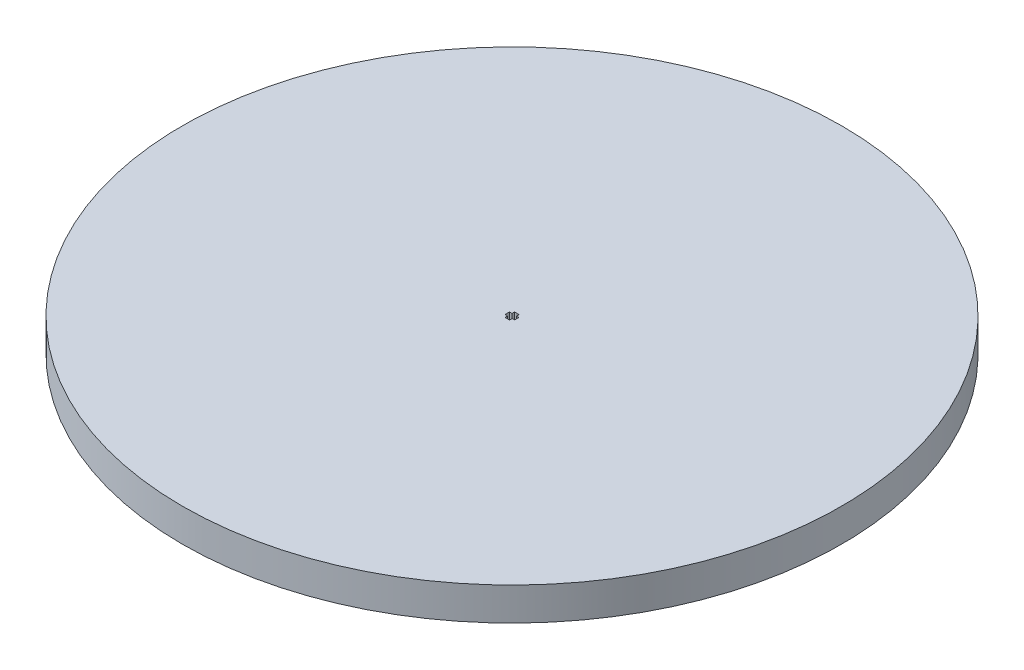
SolidWorks part; units mm, degrees
ref_plane "Front Plane" through (0, 0, 0) normal (0, 0, 1) x (1, 0, 0)
ref_plane "Top Plane" through (0, 0, 0) normal (0, 1, 0) x (1, 0, 0)
ref_plane "Right Plane" through (0, 0, 0) normal (1, 0, 0) x (0, 0, -1)
sketch "Sketch1" plane through (0, 0, 0) normal (0, 1, 0) x (1, 0, 0)
  line L1 (-102.886, 0) -> (102.886, 0) construction
  line L4 (-24.7302, 24.7302) -> (24.7302, -24.7302) construction
  line L5 (-31.3406, -31.3406) -> (31.3406, 31.3406) construction
  line L20 (-0.3381, -0.7219) -> (-0.3381, 0.7219)
  line L21 (-0.3381, 0.7219) -> (0.0122, 0.7219)
  line L22 (0, 0.3381) -> (-0.7219, 0.3381)
  line L23 (-0.7219, 0.3381) -> (-0.7219, -0.0122)
  line L24 (0.7329, 0.3136) -> (0.7211, -0.0365)
  line L25 (0.0114, 0.3379) -> (0.7329, 0.3136)
  line L26 (0.3379, -0.0114) -> (0.3622, 0.7101)
  line L27 (0.3622, 0.7101) -> (0.0122, 0.7219)
  line L28 (-0.7219, -0.3381) -> (-0.7219, 0.0122)
  line L29 (0, -0.3381) -> (-0.7219, -0.3381)
  line L30 (-0.3381, -0.7219) -> (0.0122, -0.7219)
  line L31 (0.3622, -0.7101) -> (0.0122, -0.7219)
  line L32 (0.7329, -0.3136) -> (0.7211, 0.0365)
  line L33 (0.3379, 0.0114) -> (0.3622, -0.7101)
  line L34 (0.0114, -0.3379) -> (0.7329, -0.3136)
  circle A0 centre (0, 0) radius 50
  point P4 (0, 0)
  point P7 (0, 0)
  point P15 (0, 0)
  point P18 (0, 0)
  point P50 (-0.3381, 0)
extrude "Boss-Extrude1" add sketch "Sketch1" along normal blind 5
